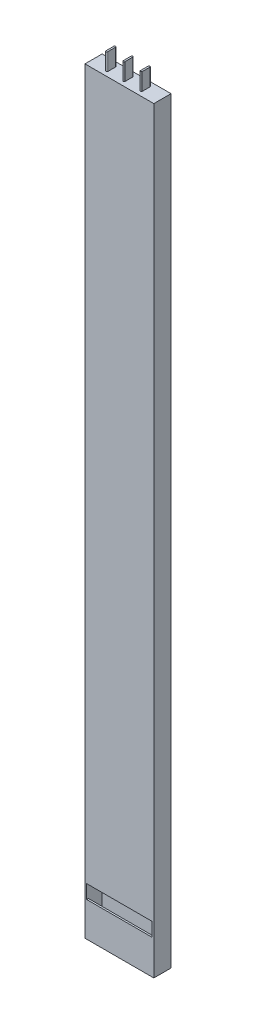
SolidWorks part; units mm, degrees
ref_plane "Front Plane" through (0, 0, 0) normal (0, 0, 1) x (1, 0, 0)
ref_plane "Top Plane" through (0, 0, 0) normal (0, 1, 0) x (1, 0, 0)
ref_plane "Right Plane" through (0, 0, 0) normal (1, 0, 0) x (0, 0, -1)
sketch "Sketch2" plane through (0, 0, 0) normal (0, 1, 0) x (1, 0, 0)
  line L1 (-20, -5) -> (20, -5)
  line L2 (-20, -5) -> (-20, 5)
  line L3 (-20, 5) -> (20, 5)
  line L4 (20, -5) -> (20, 5)
  line L5 (-20, -5) -> (20, 5) construction
  line L6 (-20, 5) -> (20, -5) construction
  point P0 (0, 0)
extrude "Boss-Extrude2" add sketch "Sketch2" along normal blind 440
sketch "Sketch3" plane through (0, 0, 0) normal (0, 1, 0) x (1, 0, 0)
  line L1 (-19, -4) -> (19, -4)
  line L2 (-19, -4) -> (-19, 4)
  line L3 (-19, 4) -> (19, 4)
  line L4 (19, -4) -> (19, 4)
  line L5 (-19, -4) -> (19, 4) construction
  line L6 (-19, 4) -> (19, -4) construction
  point P0 (0, 0)
extrude "Cut-Extrude1" cut sketch "Sketch3" along normal blind 438
sketch "Sketch4" plane through (0, 440, 0) normal (0, 1, 0) x (1, 0, 0)
  line L0 (-20, 5) -> (-20, -5) construction
  line L2 (-10.5, -2.25) -> (-10.5, 2.25)
  line L3 (-9.5, -2.25) -> (-9.5, 2.25)
  arc A0 (-9.5, -2.25) -> (-10.5, -2.25) centre (-10, -2.25) cw
  arc A1 (-10.5, 2.25) -> (-9.5, 2.25) centre (-10, 2.25) cw
  point P0 (-10, 0)
  point P6 (-10, 0)
  point P7 (-10, 0)
  point P9 (-10.5, 0)
  point P13 (-9.5, 0)
  dimension "D1" = 10
extrude "Boss-Extrude4" add sketch "Sketch4" along normal blind 10
pattern_linear "LPattern2" count 3 spacing 10 along (1, 0, 0) of "Boss-Extrude4"
ref_plane "Plane1" through (0, 0, 0) normal (0, -1, 0) x (-1, 0, 0)
sketch "Sketch5" plane through (0, 0, 0) normal (0, -1, 0) x (-1, 0, 0)
  line L1 (-19, -4) -> (19, -4)
  line L2 (-19, -4) -> (-19, 4)
  line L3 (-19, 4) -> (19, 4)
  line L4 (19, -4) -> (19, 4)
  line L5 (-19, -4) -> (19, 4) construction
  line L6 (-19, 4) -> (19, -4) construction
  point P0 (0, 0)
extrude "Boss-Extrude5" add sketch "Sketch5" against normal blind 12
sketch "Sketch6" plane through (0, 0, 0) normal (0, -1, 0) x (1, 0, 0)
  line L0 (20, 5) -> (20, -5) construction
  line L2 (10.5, 2.25) -> (10.5, -2.25)
  line L3 (9.5, 2.25) -> (9.5, -2.25)
  arc A0 (10.5, -2.25) -> (9.5, -2.25) centre (10, -2.25) cw
  arc A1 (9.5, 2.25) -> (10.5, 2.25) centre (10, 2.25) cw
  point P0 (20, 0)
  point P1 (10, 0)
  point P8 (10, 0)
  point P11 (10.5, 0)
  point P14 (9.5, 0)
  dimension "D1" = 10
extrude "Cut-Extrude2" cut sketch "Sketch6" against normal blind 11 contours L3 A0 L2 A1
pattern_linear "LPattern3" count 3 spacing 10 along (-1, 0, 0) of "Cut-Extrude2"
sketch "Sketch7" plane through (0, 0, 5) normal (0, 0, 1) x (1, 0, 0)
  line L8 (0, 29) -> (0, 19) construction
  line L9 (-20, 29) -> (20, 29) construction
  line L10 (-20, 19) -> (20, 19) construction
  line L12 (-19, 20) -> (19, 20)
  line L13 (-19, 20) -> (-19, 28)
  line L14 (-19, 28) -> (19, 28)
  line L15 (19, 20) -> (19, 28)
  line L16 (-19, 20) -> (19, 28) construction
  line L17 (-19, 28) -> (19, 20) construction
  point P6 (0, 24)
  point P7 (0, 24)
extrude "Cut-Extrude3" cut sketch "Sketch7" against normal blind 5
